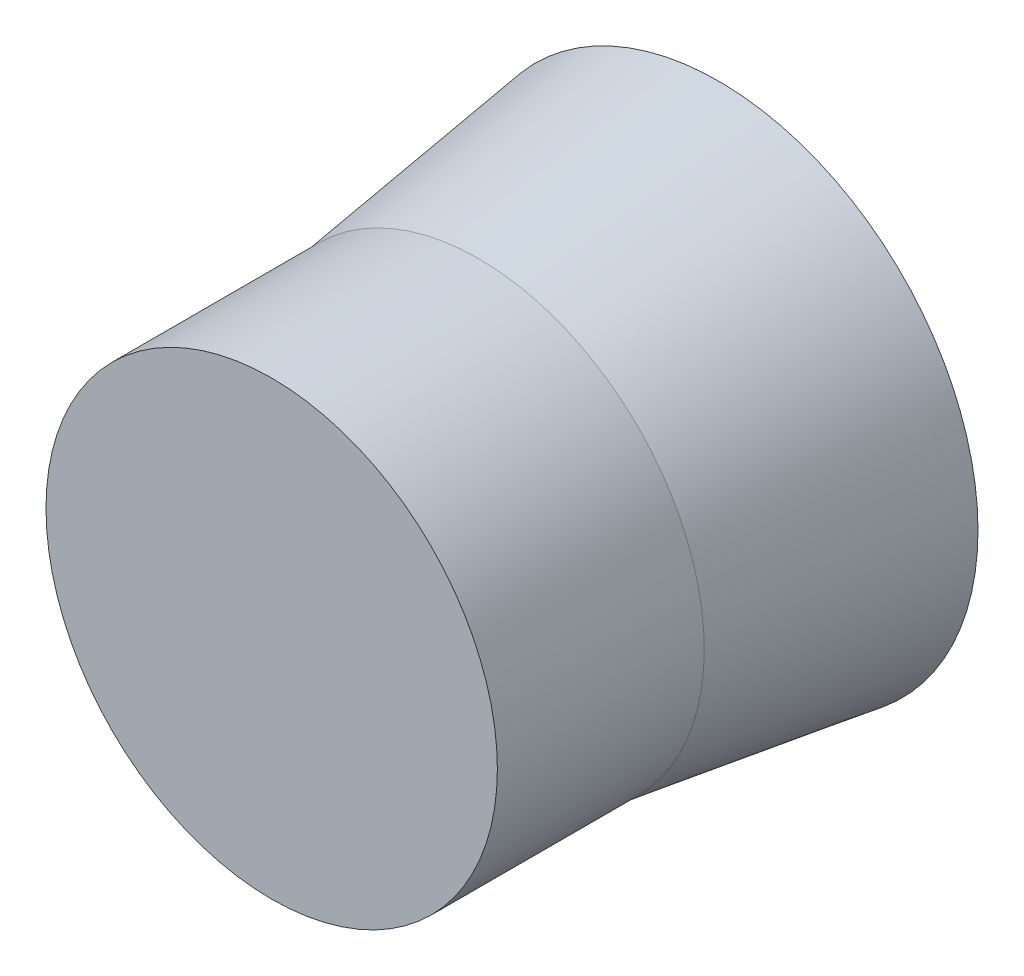
SolidWorks part; units mm, degrees
ref_plane "Front Plane" through (0, 0, 0) normal (0, 0, 1) x (1, 0, 0)
ref_plane "Top Plane" through (0, 0, 0) normal (0, 1, 0) x (1, 0, 0)
ref_plane "Right Plane" through (0, 0, 0) normal (1, 0, 0) x (0, 0, -1)
sketch "Sketch1" plane through (0, 0, 0) normal (1, 0, 0) x (0, 0, -1)
  line L0 (-1361.5784, -2.1841) -> (-138.2451, -2.1841) construction
  line L1 (0, 0) -> (111.3498, 0) construction
  line L2 (-40.9829, 63.6653) -> (-131.7124, 63.6653) construction
  line L3 (0, 0) -> (0, 50.2621)
  line L4 (0, 50.2621) -> (99.4931, 57.7369)
  line L5 (99.4931, 57.7369) -> (99.4931, 21.1358)
  line L6 (99.4931, 21.1358) -> (111.3498, 16.2385)
  line L7 (111.3498, 16.2385) -> (111.3498, 0)
  line L8 (0, 105) -> (207.8462, 120.6154)
  line L9 (0, 0) -> (0, 105)
  line L10 (232.6154, 33.9231) -> (232.6154, 0)
  line L11 (207.8462, 120.6154) -> (207.8462, 44.1538)
  line L12 (0, 0) -> (232.6154, 0) construction
  line L13 (207.8462, 44.1538) -> (232.6154, 33.9231)
  dimension "D1" = 63.6653
sketch "Sketch2" plane through (0, 0, 0) normal (1, 0, 0) x (0, 0, -1)
  line L0 (0, 0) -> (232, 0)
  line L1 (0, 105) -> (96.258, 105)
  line L2 (96.258, 105) -> (208, 120.6154)
  line L8 (0, 0) -> (0, 105)
  line L9 (232, 34) -> (232, 0)
  line L10 (208, 120.6154) -> (208, 44.6154)
  line L11 (0, 0) -> (232, 0) construction
  line L12 (208, 44.6154) -> (232, 34)
  dimension "D1" = 105
  dimension "D2" = 232
  dimension "D3" = 76
  dimension "D4" = 34
  dimension "D5" = 24
revolve "Revolve1" add sketch "Sketch2" angle 360 about L11
